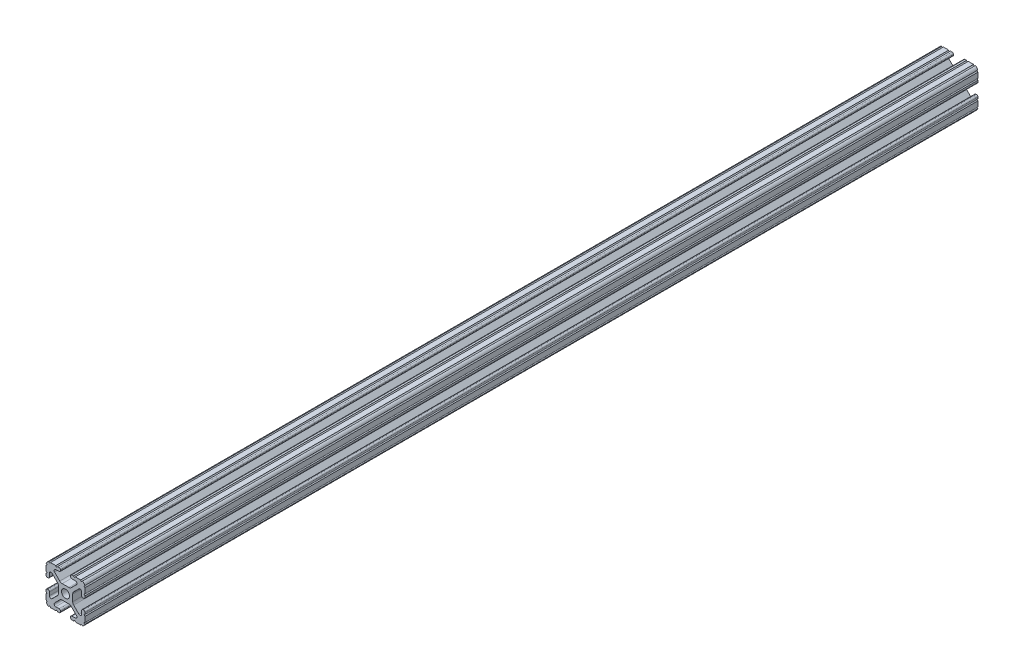
SolidWorks part; units mm, degrees
ref_plane "Front Plane" through (0, 0, 0) normal (0, 0, 1) x (1, 0, 0)
ref_plane "Top Plane" through (0, 0, 0) normal (0, 1, 0) x (1, 0, 0)
ref_plane "Right Plane" through (0, 0, 0) normal (1, 0, 0) x (0, 0, -1)
sketch "Sketch2" plane through (0, 0, 0) normal (0, 0, 1) x (1, 0, 0)
  line L0 (0, 12.7) -> (0, -12.7) construction
  line L1 (-12.7, 0) -> (12.7, 0) construction
  line L2 (3.2512, -12.7) -> (12.7, -12.7)
  line L3 (12.7, -12.7) -> (12.7, -3.2512)
  line L4 (3.2512, -12.7) -> (3.2512, -10.4902)
  line L5 (3.2512, -10.4902) -> (8.9276, -10.4902)
  line L6 (8.9276, -10.4902) -> (3.0856, -4.6482)
  line L7 (0, 0) -> (12.7, -12.7) construction
  line L8 (12.7, -3.2512) -> (10.4902, -3.2512)
  line L9 (10.4902, -3.2512) -> (10.4902, -8.9276)
  line L10 (10.4902, -8.9276) -> (4.6482, -3.0856)
  circle A0 centre (0, 0) radius 2.6035
  arc A1 (6.3485, -10.4902) -> (7.1039, -8.6665) centre (6.3485, -9.4219) ccw construction
  point P8 (0, -4.6482)
  dimension "Center Hole Diameter" = 5.207
  dimension "Rail Height" = 25.4
  dimension "Rail Width" = 25.4
  dimension "T-Slot Width" = 6.5024
  dimension "Slot Inner Width" = 14.8336
  dimension "Thickness" = 2.2098
  dimension "Slot Depth" = 5.842
  dimension "D1" = 2.2098
sketch "Sketch3" plane through (0, 0, 0) normal (1, 0, 0) x (0, 0, -1)
  line L0 (-304.8, -12.7) -> (304.8, -12.7) construction
  line L1 (-279.4, 0) -> (279.4, 0) construction
  dimension "Length" = 609.6
  dimension "D1" = 25.4
sketch "Sketch4" plane through (0, 0, 0) normal (0, 0, 1) x (1, 0, 0)
  line L0 (4.1904, -12.7) -> (10.1173, -12.7)
  line L1 (3.2512, -12.7) -> (12.7, -12.7) construction
  line L2 (3.2512, -12.7) -> (3.2512, -10.4902) construction
  line L3 (3.2512, -10.4902) -> (8.9276, -10.4902) construction
  line L4 (3.2512, -11.4294) -> (3.2512, -11.7608)
  line L5 (4.1904, -10.4902) -> (6.3485, -10.4902)
  line L6 (0, -4.6482) -> (2.164, -4.6482)
  line L7 (8.9276, -10.4902) -> (3.0856, -4.6482) construction
  line L8 (3.7373, -5.2999) -> (7.1039, -8.6665)
  line L9 (12.7, -12.7) -> (12.7, -3.2512) construction
  line L10 (10.4902, -8.9276) -> (4.6482, -3.0856) construction
  line L11 (10.4902, -3.2512) -> (10.4902, -8.9276) construction
  line L12 (10.4902, -6.3485) -> (10.4902, -4.1904)
  line L13 (12.7, -3.2512) -> (10.4902, -3.2512) construction
  line L14 (11.4294, -3.2512) -> (11.7608, -3.2512)
  line L15 (12.7, -4.1904) -> (12.7, -10.1173)
  line L16 (8.6665, -7.1039) -> (5.2999, -3.7373)
  line L17 (4.6482, 0) -> (4.6482, -2.164)
  line L18 (-12.7, 0) -> (12.7, 0) construction
  line L19 (0, -4.6482) -> (0, -2.6035)
  line L20 (0, 12.7) -> (0, -12.7) construction
  line L21 (4.6482, 0) -> (2.6035, 0)
  arc A0 (3.2512, -11.7608) -> (4.1904, -12.7) centre (4.1904, -11.7608) ccw
  arc A2 (3.2512, -11.4294) -> (4.1904, -10.4902) centre (4.1904, -11.4294) cw
  arc A3 (6.3485, -10.4902) -> (7.1039, -8.6665) centre (6.3485, -9.4219) ccw
  arc A4 (2.164, -4.6482) -> (3.7373, -5.2999) centre (2.164, -6.8732) cw
  arc A5 (10.1173, -12.7) -> (12.7, -10.1173) centre (10.1173, -10.1173) ccw
  arc A6 (8.6665, -7.1039) -> (10.4902, -6.3485) centre (9.4219, -6.3485) ccw
  arc A7 (10.4902, -4.1904) -> (11.4294, -3.2512) centre (11.4294, -4.1904) cw
  arc A8 (11.7608, -3.2512) -> (12.7, -4.1904) centre (11.7608, -4.1904) cw
  arc A9 (5.2999, -3.7373) -> (4.6482, -2.164) centre (6.8732, -2.164) cw
  circle A10 centre (0, 0) radius 2.6035 construction
  arc A11 (0, -2.6035) -> (2.6035, 0) centre (0, 0) ccw
  dimension "D1" = 2.5827
  dimension "D2" = 2.225
  dimension "D3" = 0.9392
extrude "Boss-Extrude1" add sketch "Sketch4" along normal mid plane 609.6
sketch "Sketch5" plane through (0, 0, 0) normal (0, 0, 1) x (1, 0, 0)
  line L0 (3.2512, -12.7) -> (12.7, -12.7) construction
  line L1 (4.1904, -10.4902) -> (6.3485, -10.4902) construction
  line L3 (0, 0) -> (12.7, -12.7) construction
  line L4 (6.3485, -10.4902) -> (6.3485, -12.7) construction
  line L5 (8.9276, -10.4902) -> (3.0856, -4.6482) construction
  circle A0 centre (10.3562, -12.7) radius 0.5524
  circle A1 centre (5.796, -12.7) radius 0.5524
  circle A2 centre (12.7, -10.3562) radius 0.5524
  circle A3 centre (12.7, -5.796) radius 0.5524
  point P10 (5.2694, -10.4902)
  point P12 (9.4219, -6.3485)
  dimension "D1" = 1.1049
extrude "Cut-Extrude1" cut sketch "Sketch5" against normal through all both and the other way through all
mirror "Mirror1" about plane through (0, 0, 0) normal (1, 0, 0) of bodies 137 134
mirror "Mirror2" about plane through (0, 0, 0) normal (0, 1, 0) of bodies 135
sketch "Sketch6" plane through (12.7, 0, 0) normal (1, 0, 0) x (0, 0, -1)
  line L0 (-304.8, 9.8037) -> (-304.8, 6.3485) construction
  line L1 (-304.8, 29.2503) -> (-276.03, 29.2503)
  line L2 (-304.8, 29.2503) -> (-304.8, -46.2084)
  line L3 (-304.8, -46.2084) -> (-276.03, -46.2084)
  line L4 (-276.03, 29.2503) -> (-276.03, -46.2084)
  line L5 (304.8, 9.8037) -> (304.8, 6.3485) construction
  dimension "D1" = 580.83
extrude "Cut-Extrude2" cut sketch "Sketch6" against normal blind 60 contours L2 L1 L4 L3
equation "\"D1@Boss-Extrude1\"=\"Length@Sketch3\""
equation "\"D1@Sketch2\"=\"Thickness@Sketch2\""
equation "\"D2@Sketch4\"=\"Slot Inner Width@Sketch2\"*0.15"
equation "\"D1@Sketch4\"=\"D3@Sketch4\"*2.75"
equation "\"D3@Sketch4\"=\"Thickness@Sketch2\"*0.425"
equation "\"D1@Sketch5\"=\"Thickness@Sketch2\"*0.5"
